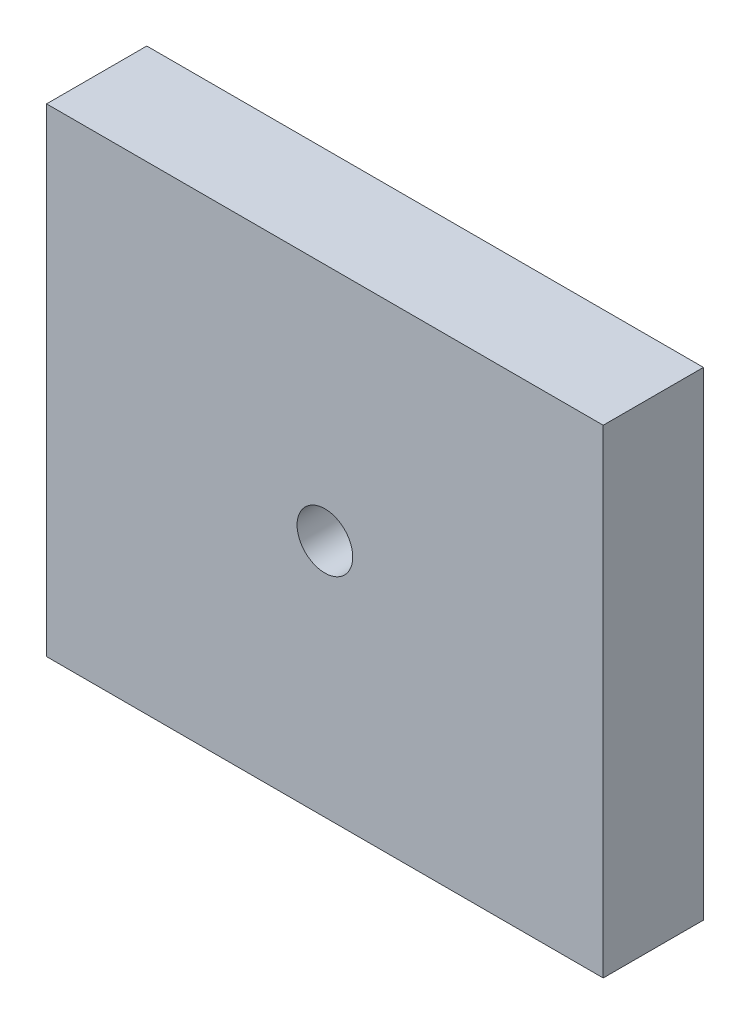
SolidWorks part; units mm, degrees
ref_plane "Plan de face" through (0, 0, 0) normal (0, 0, 1) x (1, 0, 0)
ref_plane "Plan de dessus" through (0, 0, 0) normal (0, 1, 0) x (1, 0, 0)
ref_plane "Plan de droite" through (0, 0, 0) normal (1, 0, 0) x (0, 0, -1)
sketch "Esquisse3" plane through (0, 0, 0) normal (0, 0, 1) x (1, 0, 0)
  line L1 (0, 0) -> (50, 0)
  line L2 (0, 0) -> (0, 43)
  line L3 (0, 43) -> (50, 43)
  line L4 (50, 0) -> (50, 43)
  dimension "D1" = 50
  dimension "D2" = 43
extrude "Boss.-Extru.1" add sketch "Esquisse3" along normal blind 9
sketch "Esquisse4" plane through (0, 0, 9) normal (0, 0, 1) x (1, 0, 0)
  line L0 (25, 0) -> (25, 43) construction
  line L1 (0, 0) -> (50, 0) construction
  line L2 (50, 43) -> (0, 43) construction
  circle A0 centre (25, 21.5) radius 2.5
  dimension "D1" = 5
extrude "Enlèv. mat.-Extru.1" cut sketch "Esquisse4" against normal through all both and the other way through all
sketch "Esquisse5" [suppressed] plane through (0, 0, 9) normal (0, 0, 1) x (1, 0, 0)
  line L0 (25, 0) -> (25, 48) construction
  line L1 (0, 0) -> (50, 0) construction
  line L2 (50, 48) -> (0, 48) construction
  circle A0 centre (25, 24) radius 6
  dimension "D1" = 12
extrude "Enlèv. mat.-Extru.2" [suppressed] cut sketch "Esquisse5" against normal through all both and the other way through all
